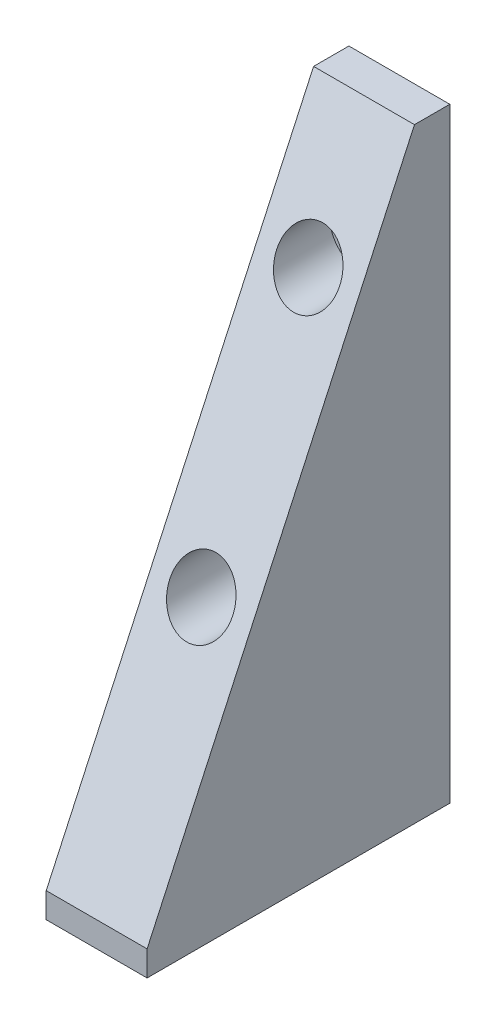
SolidWorks part; units mm, degrees
ref_plane "Front Plane" through (0, 0, 0) normal (0, 0, 1) x (1, 0, 0)
ref_plane "Top Plane" through (0, 0, 0) normal (0, 1, 0) x (1, 0, 0)
ref_plane "Right Plane" through (0, 0, 0) normal (1, 0, 0) x (0, 0, -1)
sketch "Sketch1" plane through (0, 0, 0) normal (1, 0, 0) x (0, 0, -1)
  line L0 (21.526, 126.619) -> (-45.784, -19.431)
  line L1 (-45.784, -25.781) -> (30.416, -25.781)
  line L2 (30.416, -25.781) -> (30.416, 126.619)
  line L3 (30.416, 88.4519) -> (3.9359, 88.4519) construction
  line L4 (21.526, 126.619) -> (30.416, 126.619)
  line L5 (-45.784, -19.431) -> (-45.784, -25.781)
  line L6 (30.416, 59.5647) -> (-9.3773, 59.5647) construction
  dimension "D1" = 76.2
  dimension "D2" = 152.4
  dimension "D3" = 8.89
  dimension "D4" = 6.35
extrude "Boss-Extrude2" add sketch "Sketch1" along normal blind 25.4
sketch "Sketch2" plane through (0, 0, 0) normal (-1, 0, 0) x (0, 0, 1)
  line L0 (-30.416, 96.139) -> (-11.366, 96.139) construction
  line L2 (-30.416, -25.781) -> (-30.416, 126.619) construction
  line L3 (-30.416, 37.719) -> (-10.096, 37.719) construction
  line L4 (-30.416, 126.619) -> (-21.526, 126.619) construction
  point P8 (-25.971, 126.619)
  dimension "D1" = 30.48
  dimension "D2" = 88.9
  dimension "D3" = 19.05
  dimension "D4" = 20.32
ref_plane "Plane1" through (0, 96.139, -11.366) normal (0, 0, 1) x (1, 0, 0)
ref_plane "Plane2" through (0, 37.719, -10.096) normal (0, 0, 1) x (1, 0, 0)
hole_wizard "CBORE for 3/8 Socket Head Cap Screw1" positions "Sketch3" profile "Sketch4" counterbore size "3/8" standard "ANSI Inch"
sketch "Sketch3" plane through (0, 96.139, -11.366) normal (0, 0, 1) x (1, 0, 0)
  line L0 (0, 30.48) -> (0, -115.57) construction
  line L1 (25.4, 30.48) -> (0, 30.48) construction
  point P0 (12.7, 0)
  point P8 (12.7, 30.48)
  dimension "D1" = 12.7
  dimension "D2" = 30.48
sketch "Sketch4" plane through (12.7, 96.139, -11.366) normal (1, 0, 0) x (0, -1, 0)
  line L0 (0, 0) -> (0, 19.05)
  line L1 (0, 19.05) -> (4.9022, 19.05)
  line L3 (4.9022, 19.05) -> (4.9022, 9.525)
  line L4 (4.9022, 9.525) -> (7.9375, 9.525)
  line L5 (7.9375, 9.525) -> (7.9375, 0)
  line L7 (7.9375, 0) -> (0, 0)
  line L11 (0, -6.35) -> (0, 107.95) construction
  dimension "Thru Hole Dia." = 9.8044
  dimension "Thru Hole Depth" = 19.05
  dimension "C'Bore Dia." = 15.875
  dimension "C'Bore Depth" = 9.525
hole_wizard "CBORE for 3/8 Socket Head Cap Screw2" positions "Sketch5" profile "Sketch6" counterbore size "3/8" standard "ANSI Inch"
sketch "Sketch5" plane through (0, 37.719, -10.096) normal (0, 0, 1) x (1, 0, 0)
  line L0 (0, -63.5) -> (0, 88.9) construction
  line L3 (25.4, 88.9) -> (0, 88.9) construction
  point P0 (12.7, 0)
  point P13 (12.7, 88.9)
  dimension "D1" = 12.7
  dimension "D2" = 88.9
sketch "Sketch6" plane through (12.7, 37.719, -10.096) normal (1, 0, 0) x (0, -1, 0)
  line L0 (0, 0) -> (0, 20.32)
  line L1 (0, 20.32) -> (4.9022, 20.32)
  line L3 (4.9022, 20.32) -> (4.9022, 9.525)
  line L4 (4.9022, 9.525) -> (7.9375, 9.525)
  line L5 (7.9375, 9.525) -> (7.9375, 0)
  line L7 (7.9375, 0) -> (0, 0)
  line L11 (0, -6.35) -> (0, 107.95) construction
  dimension "Thru Hole Dia." = 9.8044
  dimension "Thru Hole Depth" = 20.32
  dimension "C'Bore Dia." = 15.875
  dimension "C'Bore Depth" = 9.525
sketch "Sketch7" plane through (0, 96.139, -11.366) normal (0, 0, 1) x (1, 0, 0)
  circle A0 centre (12.7, -58.42) radius 7.9375 construction
  circle A1 centre (12.7, 0) radius 7.9375 construction
  circle A2 centre (12.7, -58.42) radius 7.9375
  circle A3 centre (12.7, 0) radius 7.9375
extrude "Cut-Extrude2" cut sketch "Sketch7" along normal up to next
hole_wizard "3/8-16 Tapped Hole1" positions "3DSketch4" profile "Sketch9" tap size "3/8-16" standard "ANSI Inch"
sketch3d "3DSketch4"
  line L0 (25.4, -25.781, -30.416) -> (0, -25.781, -30.416) construction
  line L2 (0, -25.781, 45.784) -> (0, -25.781, -30.416) construction
  point P0 (12.7, -25.781, -15.176)
  point P2 (12.7, -25.781, 25.464)
  dimension "D1" = 15.24
  dimension "D2" = 40.64
  dimension "D3" = 12.7
  dimension "D4" = 12.7
sketch "Sketch9" plane through (12.7, -25.781, -15.176) normal (1, 0, 0) x (0, 0, -1)
  line L0 (0, 0) -> (0, 27.7847)
  line L1 (0, 27.7847) -> (3.9687, 25.4)
  line L2 (3.9687, 25.4) -> (3.9687, 0)
  line L5 (3.9687, 0) -> (0, 0)
  line L10 (0, 27.7847) -> (-3.9688, 25.4) construction
  line L11 (0, -6.35) -> (0, 107.95) construction
  dimension "Tap Drill Dia." = 7.9375
  dimension "Tap Drill Depth" = 25.4
  dimension "Drill Angle" = 118
cosmetic thread "Hole Thread1" parameters "D1"=20.32, "D2"=9.525
cosmetic thread "Hole Thread2" parameters "D1"=20.32, "D2"=9.525
